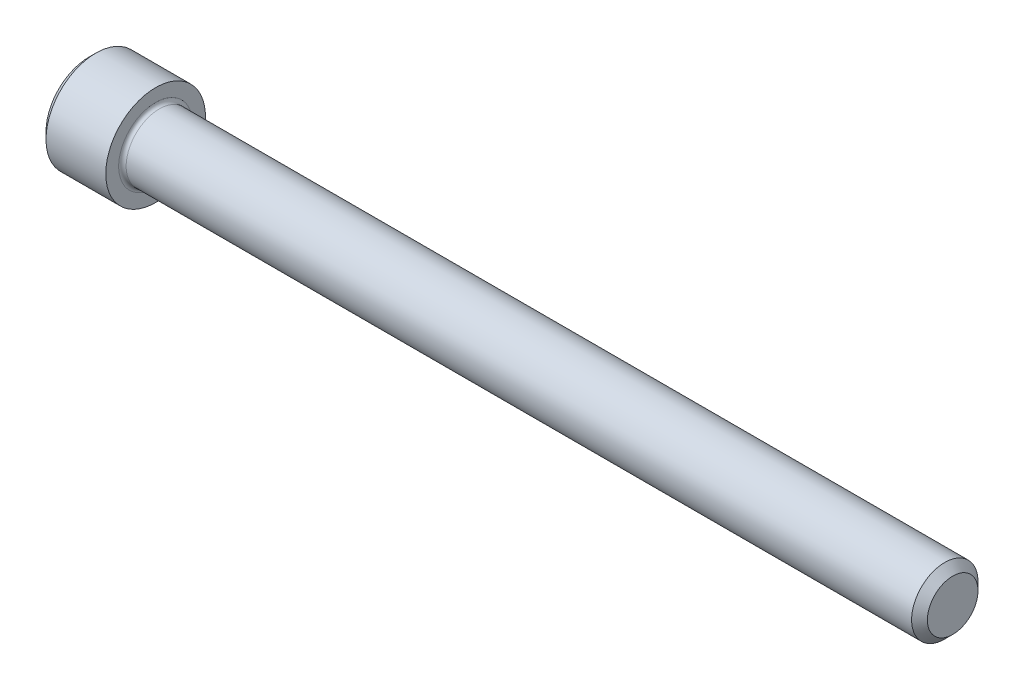
SolidWorks part; units mm, degrees
revolve "Base-Revolve" add sketch "BodySke"
sketch "BodySke" plane through (0, 0, 0) normal (0, 0, 1) x (1, 0, 0)
  line L0 (0, 0) -> (0, 4.1275)
  line L1 (0.635, 4.7625) -> (6.35, 4.7625)
  line L2 (6.35, 4.7625) -> (6.35, 3.175)
  line L3 (6.35, 3.175) -> (81.7943, 3.175)
  line L4 (82.55, 2.4193) -> (82.55, 0)
  line L5 (82.55, 0) -> (0, 0)
  line L6 (-31.75, 0) -> (127, 0) construction
  line L7 (0, 4.1275) -> (0.635, 4.7625)
  line L8 (82.55, 2.4193) -> (81.7943, 3.175)
  line L9 (0, -4.1275) -> (0.635, -4.7625) construction
  line L10 (82.55, -2.4193) -> (81.7943, -3.175) construction
  line L11 (7.62, 9.525) -> (7.62, 3.175) construction
  line L12 (57.15, 9.525) -> (57.15, 3.175) construction
  line L13 (44.45, 9.525) -> (44.45, 3.175) construction
  dimension "Diameter" = 6.35
  dimension "Head_ht" = 6.35
  dimension "Length" = 76.2
  dimension "Body_ch_ang" = 45
  dimension "Head_dia" = 9.525
  dimension "Head_ch_ang" = 45
  dimension "Head_side_ht" = 5.715
  dimension "Minor_dia" = 4.8387
  dimension "Advance" = 1.27
  dimension "Thread_nom" = 25.4
  dimension "Thread_length" = 38.1
cosmetic thread "ThreadCosmetic"
fillet "Fillet1" radius 0.3556 1 edges at (6.35, 0, 3.175)
ref_plane "Plane1" through (0, 0, 0) normal (0, 0, 1) x (1, 0, 0)
ref_plane "Plane2" through (0, 0, 0) normal (0, 1, 0) x (1, 0, 0)
ref_plane "Plane3" through (0, 0, 0) normal (1, 0, 0) x (0, 0, -1)
sketch "Sketch2" plane through (0, 0, 0) normal (0, 0, 1) x (1, 0, 0)
  line L0 (0, 2.3813) -> (3.048, 2.3813)
  line L1 (3.048, 2.3813) -> (4.4228, 0)
  line L2 (-31.75, 0) -> (127, 0) construction
  line L3 (4.4228, 0) -> (0, 0)
  line L4 (0, 0) -> (0, 2.3813)
  line L5 (0, 4.1275) -> (0, -4.1275) construction
  line L6 (0, 0) -> (47.625, 0) construction
  line L7 (6.35, -4.7625) -> (6.35, 4.7625) construction
  dimension "D1" = 2.3813
  dimension "D2" = 60
revolve "Hex-PreBroach" cut sketch "Sketch2" angle 360 about L6
sketch "Sketch3" plane through (0, 0, 0) normal (-1, 0, 0) x (0, 0.5, 0.866)
  line L0 (1.3748, 2.3813) -> (-1.3748, 2.3813)
  line L1 (-1.3748, 2.3813) -> (-2.7496, 0)
  line L2 (1.3748, 2.3813) -> (2.7496, 0)
  line L3 (1.3748, -2.3812) -> (2.7496, 0)
  line L4 (1.3748, -2.3812) -> (-1.3748, -2.3812)
  line L5 (-1.3748, -2.3812) -> (-2.7496, 0)
  dimension "D1" = 2.3813
  dimension "D2" = 2.3813
  dimension "Hex_size" = 4.7625
extrude "Hex" cut sketch "Sketch3" against normal blind 3.048
sketch "Sketch4" plane through (0, 0, 0) normal (-1, 0, 0) x (0, 0, 1)
  line L0 (0, 0) -> (2.8067, 0)
  line L1 (0, 0) -> (6.1484, 3.5498) construction
  line L2 (0, 0) -> (1.4033, 2.4307)
  line L3 (2.3336, 0.614) -> (2.6851, 0.817)
  line L4 (1.6986, 1.7139) -> (2.0501, 1.9169)
  arc A0 (2.3336, 0.614) -> (1.6986, 1.7139) centre (0, 0) ccw
  arc A1 (2.8067, 0) -> (2.6851, 0.817) centre (0, 0) ccw
  arc A2 (1.4033, 2.4307) -> (2.0501, 1.9169) centre (0, 0) cw
  dimension "D1" = 30
  dimension "D2" = 60
  dimension "Spline_p_dim" = 1.27
  dimension "D3" = 0.635
extrude "Spline" [suppressed] cut sketch "Sketch4" against normal blind 3.048
pattern_circular "CirPattern1" [suppressed] count 6 every 60
sketch "Sketch5" plane through (0, 0, 0) normal (0, 0, 1) x (1, 0, 0)
  line L0 (-31.75, 0) -> (127, 0) construction
  line L2 (0, 4.1275) -> (0, -4.1275) construction
  circle A0 centre (2.159, 0) radius 0.5905
  dimension "Drilled_hole_dia" = 1.1811
  dimension "Drilled_hole_loc" = 2.159
extrude "Hole" [suppressed] cut sketch "Sketch5" against normal through all and the other way through all
pattern_circular "Drilled-4" [suppressed] count 2 every 60
pattern_circular "Drilled-6" [suppressed] count 3 every 60
sketch "ThdSchSke" plane through (0, 0, 0) normal (0, 0, 1) x (1, 0, 0)
  line L0 (57.15, -2.4193) -> (56.6209, -3.175)
  line L1 (57.15, -2.4193) -> (57.6791, -3.175)
  line L2 (57.6791, -3.175) -> (57.6791, -3.9687)
  line L3 (-3.175, 0) -> (5.1513, 0) construction
  line L5 (57.6791, -3.9687) -> (56.6209, -3.9687)
  line L6 (56.6209, -3.9687) -> (56.6209, -3.175)
  line L7 (0, 4.1275) -> (0, -4.1275) construction
  dimension "Thread_minor" = 4.8387
  dimension "Diameter" = 6.35
  dimension "Start" = 57.15
revolve "ThreadSchematic" [suppressed] cut sketch "ThdSchSke" angle 360 about L3
pattern_linear "ThdSchPat" [suppressed]
equation "\"D2@Sketch3\" = \"Hex_size@Sketch3\" / 2"
equation "\"D1@Sketch3\" = \"Hex_size@Sketch3\" / 2"
equation "\"D1@Sketch2\" = \"Hex_size@Sketch3\" / 2"
equation "\"D3@Sketch4\" = \"Spline_p_dim@Sketch4\" / 2"
equation "\"Thread_minor@ThreadCosmetic\"  =  \"Minor_dia@BodySke\""
equation "\"D2@CirPattern1\" = 360 / \"Num_teeth@CirPattern1\""
equation "\"Wall_thickness@Sketch2\" = \"Head_ht@BodySke\" - \"Key_eng@Hex\""
equation "\"Thread_length@ThreadCosmetic\" = ((sgn( (\"Length@BodySke\" - \"Advance@BodySke\" ) - \"Thread_nom@BodySke\" )-1)*( (\"Length@BodySke\" - \"Advance@BodySke\" ) - \"Thread_nom@BodySke\" ))/-2+ \"Thread_nom@BodySke\""
equation "\"Thread_minor@ThdSchSke\" = \"Minor_dia@BodySke\""
equation "\"Diameter@ThdSchSke\" = \"Diameter@BodySke\""
equation "\"Overcut@ThdSchSke\" = \"Diameter@BodySke\" * 1.25"
equation "\"Start@ThdSchSke\" = \"Head_ht@BodySke\" + \"Length@BodySke\" - \"Thread_length@ThreadCosmetic\"  '---Non-countersunk---"
equation "\"Num_threads@ThdSchPat\" = int( \"Thread_length@ThreadCosmetic\" / \"Advance@BodySke\" + 0.999 )  + 1"
equation "\"Advance@ThdSchPat\" = \"Thread_length@ThreadCosmetic\" /  (\"Num_threads@ThdSchPat\" - 1) 'relax it"
equation "\"Num_threads@ThdSchPat\" = \"Num_threads@ThdSchPat\" - sgn( \"Num_threads@ThdSchPat\" - 1) '---chamfered tips only---"
